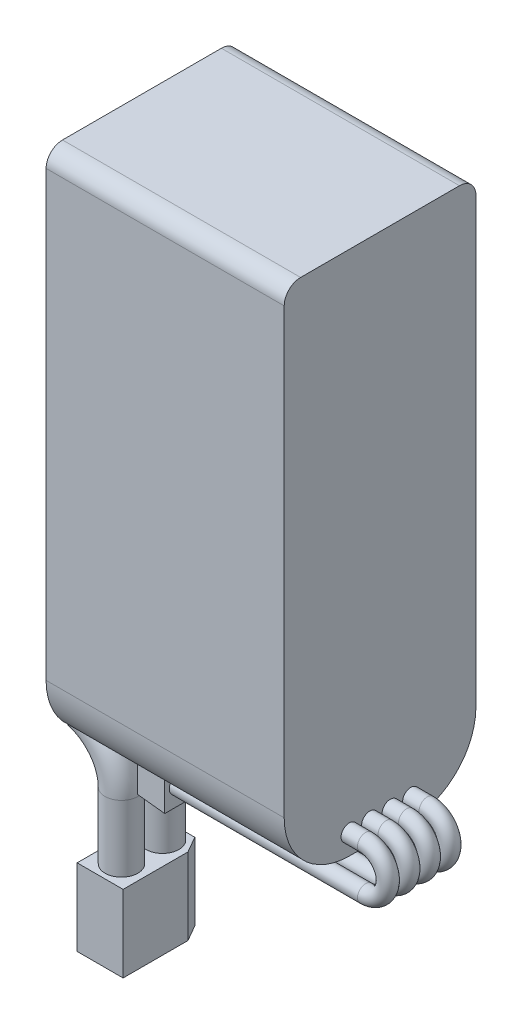
SolidWorks part; units mm, degrees
ref_plane "Front Plane" through (0, 0, 0) normal (1, 0, 0) x (0, 1, 0)
ref_plane "Top Plane" through (0, 0, 0) normal (0, 0, 1) x (0, 1, 0)
ref_plane "Right Plane" through (0, 0, 0) normal (0, 1, 0) x (-1, 0, 0)
sketch "Sketch1" plane through (0, 0, 0) normal (0, 0, 1) x (0, 1, 0)
  line L1 (-32, -14.5) -> (32, -14.5)
  line L2 (-32, -14.5) -> (-32, 14.5)
  line L3 (-32, 14.5) -> (32, 14.5)
  line L4 (32, -14.5) -> (32, 14.5)
  line L5 (-32, -14.5) -> (32, 14.5) construction
  line L6 (-32, 14.5) -> (32, -14.5) construction
  point P0 (0, 0)
  dimension "D1" = 64
  dimension "D2" = 29
extrude "Boss-Extrude1" add sketch "Sketch1" along normal blind 23.35
fillet "Fillet1" radius 2 2 edges at (0, 32, 0) (0, 32, 23.35)
sketch "Sketch2" plane through (-14.5, 0, 10) normal (1, 0, 0) x (0, 0, -1)
  line L0 (0.825, -29) -> (-4.175, -29) construction
  line L2 (-1.675, -29) -> (-1.675, -20.0823) construction
  line L3 (10, 30) -> (10, -32) construction
  line L4 (-13.35, 30) -> (-13.35, -32) construction
  line L5 (10, 30) -> (10, -32) construction
  line L6 (-13.35, 30) -> (-13.35, -32) construction
  line L7 (-13.35, -32) -> (10, -32) construction
  circle A0 centre (0.825, -29) radius 2
  circle A1 centre (-4.175, -29) radius 2
  dimension "D1" = 4
  dimension "D2" = 5
  dimension "D3" = 3
sketch "Sketch4" plane through (0, 0, 0) normal (0, 0, 1) x (0, 1, 0)
  line L0 (-29, 14.5) -> (-29, 17.8115)
  line L1 (-39.8327, 14.4947) -> (-47.9299, 14.4947)
  arc A0 (-29, 17.8115) -> (-33.9722, 18.6551) centre (-31.5576, 17.8115) ccw
  arc A1 (-33.9722, 18.6551) -> (-39.8327, 14.4947) centre (-39.8327, 20.7027) cw
sweep "Sweep2" add profiles "Sketch2" path "Sketch4"
sketch "Sketch5" plane through (14.5, 0, 0) normal (1, 0, 0) x (0, 1, 0)
  line L0 (-29.5, 12.925) -> (-29.5, 10.425) construction
  line L1 (-32, 0) -> (30, 0) construction
  line L2 (-32, 23.35) -> (30, 23.35) construction
  line L3 (-32, 0) -> (30, 0) construction
  line L4 (-32, 23.35) -> (30, 23.35) construction
  line L5 (-29.5, 11.675) -> (-24.2481, 11.675) construction
  line L6 (-32, 23.35) -> (-32, 0) construction
  circle A0 centre (-29.5, 12.925) radius 1
  circle A1 centre (-29.5, 10.425) radius 1
  circle A2 centre (-29.5, 15.425) radius 1
  circle A3 centre (-29.5, 7.925) radius 1
  dimension "D1" = 2
  dimension "D2" = 2.5
  dimension "D3" = 2.5
  dimension "D4" = 2.5
  dimension "D5" = 2.5
sketch "Sketch6" plane through (0, 0, 0) normal (0, 0, 1) x (0, 1, 0)
  line L0 (-29.5, -16.4977) -> (-29.5, -14.5)
  line L1 (-34.9001, -16.4977) -> (-34.9001, 6.4232)
  arc A0 (-29.5, -16.4977) -> (-34.9001, -16.4977) centre (-32.2, -16.4977) cw
sweep "Sweep3" add profiles "Sketch5" path "Sketch6"
sketch "Sketch7" plane through (-6.4232, 0, 0) normal (-1, 0, 0) x (0, -1, 0)
  line L0 (34.9001, 11.675) -> (35.3785, 11.675) construction
  line L1 (32.6001, 6.375) -> (37.2001, 6.375)
  line L2 (32.6001, 6.375) -> (32.6001, 16.975)
  line L3 (32.6001, 16.975) -> (37.2001, 16.975)
  line L4 (37.2001, 6.375) -> (37.2001, 16.975)
  line L5 (32.6001, 6.375) -> (37.2001, 16.975) construction
  line L6 (32.6001, 16.975) -> (37.2001, 6.375) construction
  circle A0 centre (34.9001, 10.425) radius 1 construction
  circle A1 centre (34.9001, 12.925) radius 1 construction
  circle A2 centre (34.9001, 10.425) radius 1 construction
  circle A3 centre (34.9001, 12.925) radius 1 construction
  point P0 (34.9001, 11.675)
  dimension "D1" = 10.6
  dimension "D2" = 4.6
extrude "Boss-Extrude2" add sketch "Sketch7" along normal blind 3.5 draft 3
sketch "Sketch8" plane through (0, -47.9299, 0) normal (0, -1, 0) x (1, 0, 0)
  line L5 (-14.4947, 11.675) -> (-12.7903, 11.675) construction
  line L6 (-16.3531, 6.9116) -> (-12.8281, 6.9116)
  line L8 (-17.2947, 8.5426) -> (-17.2947, 16.775)
  line L9 (-17.2947, 16.775) -> (-11.6947, 16.775)
  line L10 (-11.6947, 8.8746) -> (-11.6947, 16.775)
  line L11 (-17.2947, 6.575) -> (-11.6947, 16.775) construction
  line L12 (-17.2947, 16.775) -> (-11.8318, 6.8247) construction
  line L13 (-16.3531, 6.9116) -> (-17.2947, 8.5426)
  line L14 (-12.8281, 6.9116) -> (-11.6947, 8.8746)
  circle A4 centre (-14.4947, 14.175) radius 2 construction
  circle A5 centre (-14.4947, 9.175) radius 2 construction
  circle A6 centre (-14.4947, 14.175) radius 2 construction
  circle A7 centre (-14.4947, 9.175) radius 2 construction
  point P6 (-14.4947, 11.675)
  dimension "D1" = 10.2
  dimension "D2" = 5.6
  dimension "D3" = 60
  dimension "D4" = 60
  dimension "D5" = 1
  dimension "D6" = 1
extrude "Boss-Extrude3" add sketch "Sketch8" along normal blind 9.35
fillet "Fillet3" radius 8 2 edges at (0, -32, 0) (0, -32, 23.35)
